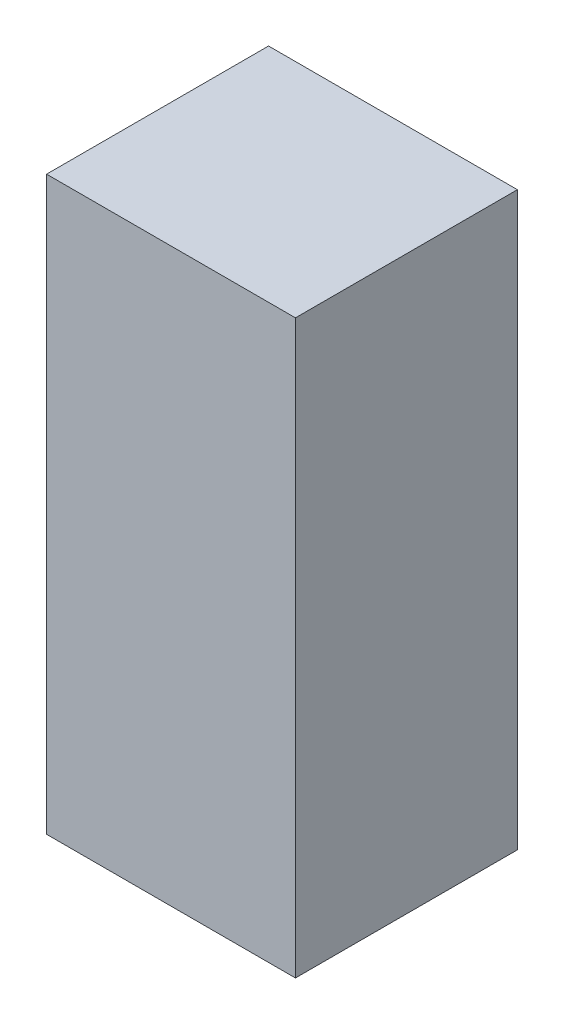
SolidWorks part; units mm, degrees
ref_plane "Alzado" through (0, 0, 0) normal (0, 0, 1) x (1, 0, 0)
ref_plane "Planta" through (0, 0, 0) normal (0, 1, 0) x (1, 0, 0)
ref_plane "Vista lateral" through (0, 0, 0) normal (1, 0, 0) x (0, 0, -1)
sketch "Croquis1" plane through (0, 0, 0) normal (0, 1, 0) x (1, 0, 0)
  line L1 (-18.5, -16.5) -> (18.5, -16.5)
  line L2 (-18.5, -16.5) -> (-18.5, 16.5)
  line L3 (-18.5, 16.5) -> (18.5, 16.5)
  line L4 (18.5, -16.5) -> (18.5, 16.5)
  line L5 (-18.5, -16.5) -> (18.5, 16.5) construction
  line L6 (-18.5, 16.5) -> (18.5, -16.5) construction
  point P0 (0, 0)
  dimension "D1" = 37
  dimension "D2" = 33
extrude "Saliente-Extruir1" add sketch "Croquis1" along normal blind 85
